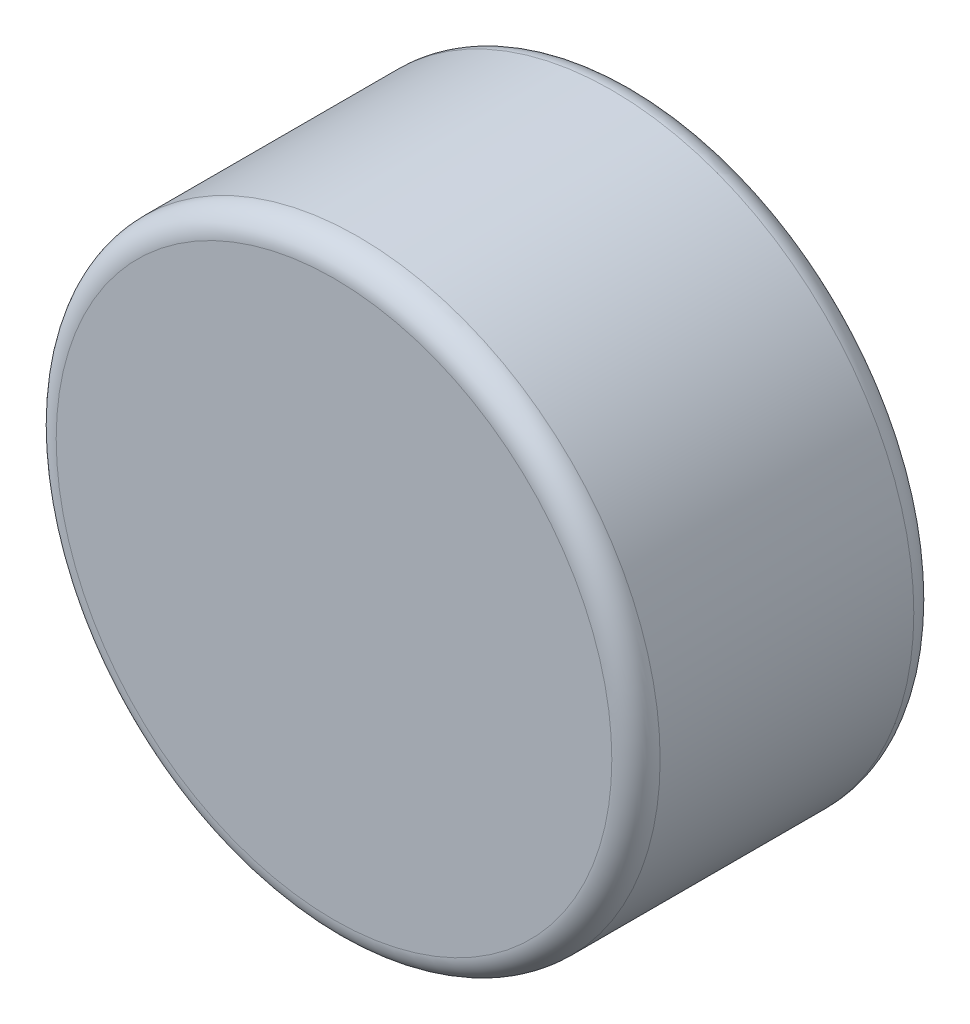
SolidWorks part; units mm, degrees
ref_plane "Piano frontale" through (0, 0, 0) normal (0, 0, 1) x (1, 0, 0)
ref_plane "Piano superiore" through (0, 0, 0) normal (0, 1, 0) x (1, 0, 0)
ref_plane "Piano destro" through (0, 0, 0) normal (1, 0, 0) x (0, 0, -1)
sketch "Schizzo1" plane through (0, 0, 0) normal (0, 0, 1) x (1, 0, 0)
  circle A0 centre (0, 0) radius 2.5
  dimension "D1" = 5
extrude "Estrusione-Estrusione1" add sketch "Schizzo1" along normal blind 2.5
fillet "Raccordo1" radius 0.2 2 edges at (2.5, 0, 0) (2.5, 0, 2.5)
equation "\"diametro_magnete\"= 6mm 'diametro magnete"
equation "\"altezza_magnete\"= 4 'altezza magnete"
equation "\"D1@Estrusione-Estrusione1\"= \"altezza_magnete\""
